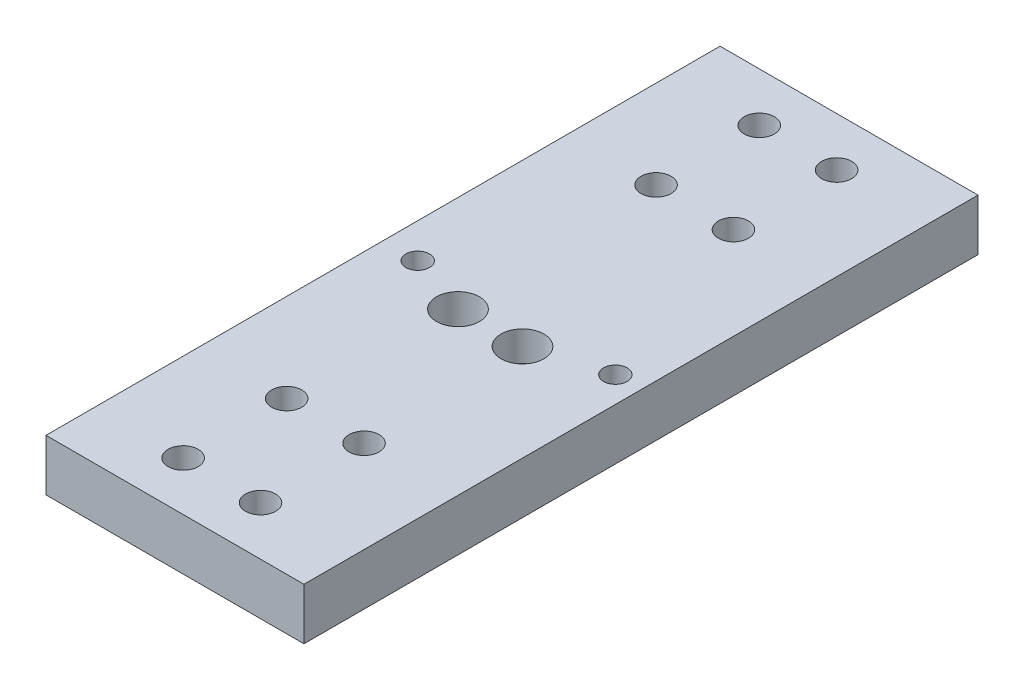
SolidWorks part; units mm, degrees
ref_plane "Front Plane" through (0, 0, 0) normal (0, 0, 1) x (1, 0, 0)
ref_plane "Top Plane" through (0, 0, 0) normal (0, 1, 0) x (1, 0, 0)
ref_plane "Right Plane" through (0, 0, 0) normal (1, 0, 0) x (0, 0, -1)
sketch "Sketch3" plane through (-27.527, 0, 0) normal (0, 1, 0) x (0, 0, 1)
  line L0 (41.3041, 73.5608) -> (-72.5469, 73.5608) construction
  line L2 (41.3041, 8.3895) -> (-72.5469, 8.3895) construction
  line L3 (31.3041, -26.6984) -> (31.3041, 62.3179) construction
  line L5 (-78.6959, -26.6984) -> (-78.6959, 62.3179) construction
  line L7 (31.3041, 62.3179) -> (-78.6959, -26.6984) construction
  line L13 (54.6906, 47.8098) -> (-102.0824, 47.8098)
  line L14 (54.6906, 47.8098) -> (54.6906, -12.1902)
  line L15 (54.6906, -12.1902) -> (-102.0824, -12.1902)
  line L16 (-102.0824, 47.8098) -> (-102.0824, -12.1902)
  line L17 (54.6906, 47.8098) -> (-102.0824, -12.1902) construction
  line L18 (54.6906, -12.1902) -> (-102.0824, 47.8098) construction
  point P2 (-23.6959, 17.8098)
  dimension "D1" = 60
extrude "Boss-Extrude6" add sketch "Sketch3" along normal blind 12
sketch "Sketch4" plane through (0, 12, 0) normal (0, 1, 0) x (1, 0, 0)
  line L0 (20.2828, 23.6959) -> (-39.7172, 23.6959) construction
  line L1 (20.2828, -54.6906) -> (20.2828, 102.0824) construction
  line L2 (-39.7172, 102.0824) -> (-39.7172, -54.6906) construction
  line L3 (20.2828, -31.3041) -> (-39.7172, -31.3041) construction
  line L4 (20.2828, 78.6959) -> (-39.7172, 78.6959) construction
  line L5 (-10.2465, -54.6906) -> (-9.7172, 102.0824) construction
  line L6 (-39.7172, -54.6906) -> (20.2828, -54.6906) construction
  line L7 (20.2828, 102.0824) -> (-39.7172, 102.0824) construction
  line L8 (20.2828, -43.3041) -> (-39.7172, -43.3041) construction
  line L9 (20.2828, -19.3041) -> (-39.7172, -19.3041) construction
  line L10 (-39.7172, 66.6959) -> (20.2828, 66.6959) construction
  line L11 (-39.7172, 90.6959) -> (20.2828, 90.6959) construction
  line L12 (-19.2081, -43.3041) -> (-19.2081, 106.6241) construction
  line L13 (-1.208, -43.3041) -> (-1.208, 116.9979) construction
  circle A2 centre (-1.127, -19.3041) radius 2.25
  circle A3 centre (-19.1271, -19.3041) radius 2.25
  circle A4 centre (-1.208, -43.3041) radius 2.25
  circle A5 centre (-19.2081, -43.3041) radius 2.25
  circle A6 centre (-19.2081, 66.6959) radius 2.25
  circle A7 centre (-19.2081, 90.6959) radius 2.25
  circle A8 centre (-1.208, 90.6959) radius 2.25
  circle A9 centre (-1.208, 66.6959) radius 2.25
  dimension "D5" = 9
  dimension "D9" = 4.5
  dimension "D12" = 4.5
  dimension "D1" = 55
  dimension "D2" = 55
  dimension "D3" = 12
  dimension "D4" = 12
  dimension "D6" = 9
  dimension "D7" = 9
  dimension "D8" = 9
  dimension "D10" = 12
  dimension "D11" = 12
extrude "Cut-Extrude1" cut sketch "Sketch4" against normal up to next
sketch "Sketch6" plane through (0, 12, 0) normal (0, 1, 0) x (1, 0, 0)
  line L3 (-9.7172, -54.6906) -> (-9.7172, 102.0824) construction
  line L4 (-39.7172, -54.6906) -> (20.2828, -54.6906) construction
  line L5 (20.2828, 102.0824) -> (-39.7172, 102.0824) construction
  line L6 (-17.2172, 18.6316) -> (-2.2172, 18.6316) construction
  circle A0 centre (-17.2172, 18.6316) radius 3.25
  circle A1 centre (-2.2172, 18.6316) radius 3.25
  point P0 (-9.7172, 18.6316)
  dimension "D1" = 6.5
  dimension "D2" = 6.5
  dimension "D3" = 15
  dimension "D4" = 73.3222
extrude "Cut-Extrude2" cut sketch "Sketch6" against normal up to next
sketch "Sketch7" plane through (0, 12, 0) normal (0, 1, 0) x (1, 0, 0)
  circle A0 centre (-19.1271, -19.3041) radius 3.5
  circle A1 centre (-19.2081, -43.3041) radius 3.5
  circle A2 centre (-1.208, -43.3041) radius 3.5
  circle A3 centre (-1.127, -19.3041) radius 3.5
  circle A4 centre (-1.208, 66.6959) radius 3.5
  circle A5 centre (-19.2081, 66.6959) radius 3.5
  circle A6 centre (-19.2081, 90.6959) radius 3.5
  circle A7 centre (-1.208, 90.6959) radius 3.5
  dimension "D1" = 7
extrude "Cut-Extrude3" cut sketch "Sketch7" against normal blind 5
sketch "Sketch8" plane through (0, 12, 0) normal (0, 1, 0) x (1, 0, 0)
  circle A0 centre (-17.2172, 18.6316) radius 5
  circle A1 centre (-2.2172, 18.6316) radius 5
  dimension "D1" = 10
  dimension "D2" = 10
extrude "Cut-Extrude4" cut sketch "Sketch8" against normal blind 7
sketch "Sketch9" plane through (0, 12, 0) normal (0, 1, 0) x (1, 0, 0)
  circle A0 centre (-31.6579, 23.7018) radius 2.75
  circle A1 centre (14.2827, 23.7357) radius 2.75
  dimension "D1" = 5.5
extrude "Cut-Extrude5" cut sketch "Sketch9" against normal up to next
sketch "Sketch10" plane through (0, 0, 0) normal (0, 1, 0) x (1, 0, 0)
  line L1 (-39.7172, 102.0824) -> (20.2828, 102.0824)
  line L2 (-39.7172, 102.0824) -> (-39.7172, -54.6906)
  line L3 (-39.7172, -54.6906) -> (20.2828, -54.6906)
  line L4 (20.2828, 102.0824) -> (20.2828, -54.6906)
  circle A0 centre (-19.2081, -43.3041) radius 2.25 construction
  circle A2 centre (-1.208, -43.3041) radius 2.25 construction
  circle A3 centre (-1.208, -43.3041) radius 3.5 construction
  circle A4 centre (-1.208, 90.6959) radius 3.5 construction
  circle A5 centre (-1.208, 90.6959) radius 2.25 construction
  circle A6 centre (-19.2081, 90.6959) radius 2.25 construction
  circle A7 centre (-19.2081, 90.6959) radius 3.5 construction
  circle A8 centre (-19.2081, 66.6959) radius 2.25 construction
  circle A9 centre (-1.208, 66.6959) radius 2.25 construction
  circle A10 centre (-1.208, 66.6959) radius 3.5 construction
  circle A11 centre (-19.2081, 66.6959) radius 3.5 construction
  circle A12 centre (-31.6579, 23.7018) radius 2.75 construction
  circle A13 centre (-17.2172, 18.6316) radius 3.25 construction
  circle A14 centre (-17.2172, 18.6316) radius 5 construction
  circle A15 centre (14.2827, 23.7357) radius 2.75 construction
  circle A16 centre (-2.2172, 18.6316) radius 3.25 construction
  circle A17 centre (-2.2172, 18.6316) radius 5 construction
  circle A18 centre (-1.127, -19.3041) radius 3.5 construction
  circle A19 centre (-1.127, -19.3041) radius 2.25 construction
  circle A20 centre (-19.1271, -19.3041) radius 2.25 construction
  circle A21 centre (-19.1271, -19.3041) radius 3.5 construction
  circle A22 centre (-19.2081, -43.3041) radius 3.5 construction
  circle A23 centre (-1.208, 90.6959) radius 3.5
  circle A24 centre (-1.208, 90.6959) radius 2.25
  circle A25 centre (-19.2081, 90.6959) radius 2.25
  circle A26 centre (-19.2081, 90.6959) radius 3.5
  circle A27 centre (-19.2081, 66.6959) radius 2.25
  circle A28 centre (-1.208, 66.6959) radius 2.25
  circle A29 centre (-1.208, 66.6959) radius 3.5
  circle A30 centre (-19.2081, 66.6959) radius 3.5
  circle A31 centre (-31.6579, 23.7018) radius 2.75
  circle A32 centre (-17.2172, 18.6316) radius 3.25
  circle A33 centre (-17.2172, 18.6316) radius 5
  circle A34 centre (14.2827, 23.7357) radius 2.75
  circle A35 centre (-2.2172, 18.6316) radius 3.25
  circle A36 centre (-2.2172, 18.6316) radius 5
  circle A37 centre (-1.127, -19.3041) radius 3.5
  circle A38 centre (-1.127, -19.3041) radius 2.25
  circle A39 centre (-19.1271, -19.3041) radius 2.25
  circle A40 centre (-19.1271, -19.3041) radius 3.5
  circle A41 centre (-19.2081, -43.3041) radius 2.25
  circle A42 centre (-19.2081, -43.3041) radius 3.5
  circle A43 centre (-1.208, -43.3041) radius 2.25
  circle A44 centre (-1.208, -43.3041) radius 3.5
